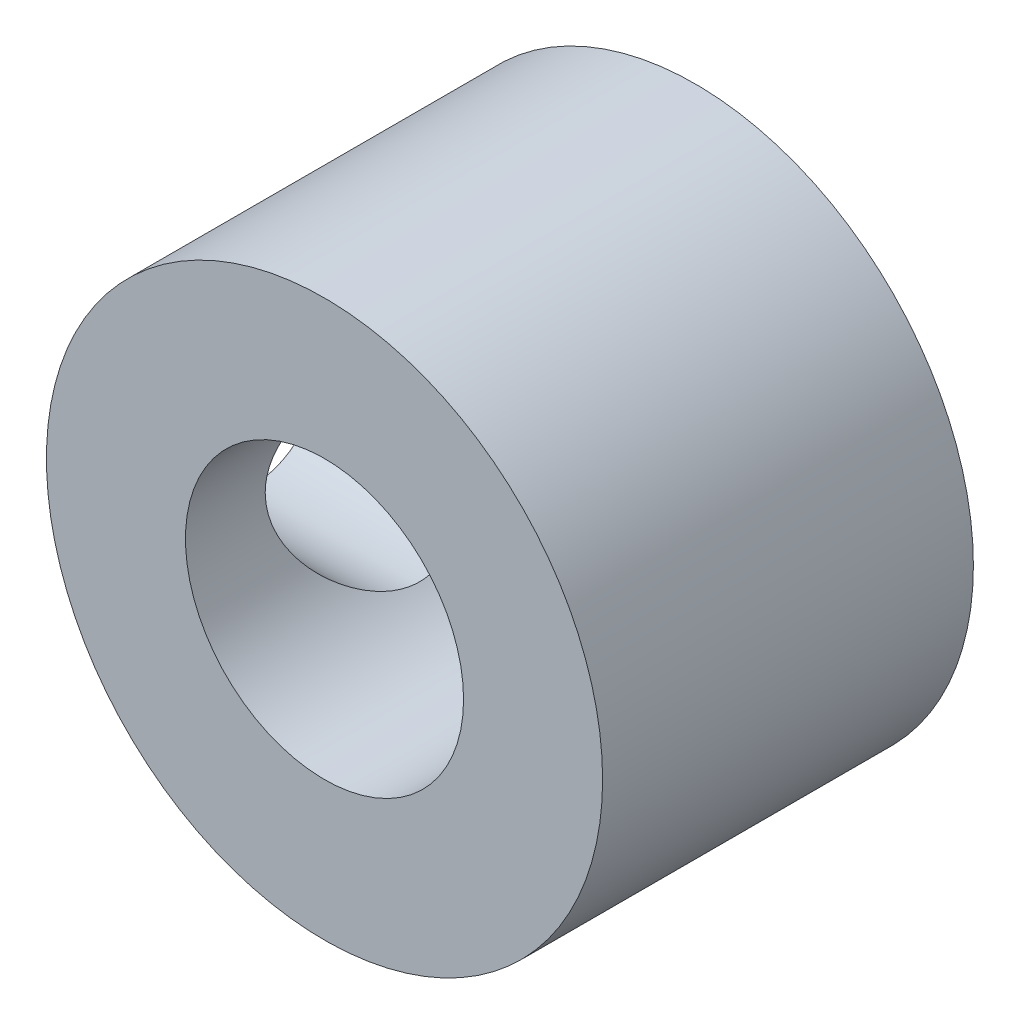
SolidWorks part; units mm, degrees
ref_plane "Front Plane" through (0, 0, 0) normal (0, 0, 1) x (1, 0, 0)
ref_plane "Top Plane" through (0, 0, 0) normal (0, 1, 0) x (1, 0, 0)
ref_plane "Right Plane" through (0, 0, 0) normal (1, 0, 0) x (0, 0, -1)
sketch "Sketch1" plane through (0, 0, 0) normal (0, 0, 1) x (1, 0, 0)
  circle A0 centre (0, 0) radius 3.175
  circle A1 centre (0, 0) radius 6.35
  dimension "D1" = 6.35
  dimension "D2" = 12.7
extrude "Boss-Extrude1" add sketch "Sketch1" along normal blind 8.4667
sketch "Sketch2" plane through (0, 0, 0) normal (1, 0, 0) x (0, 0, -1)
  line L0 (0, 0) -> (-8.4667, 0) construction
  line L1 (-8.4667, 6.35) -> (-8.4667, -6.35) construction
  circle A0 centre (-4.2333, 0) radius 2.413
  dimension "D1" = 4.826
extrude "Cut-Extrude1" cut sketch "Sketch2" against normal through all
